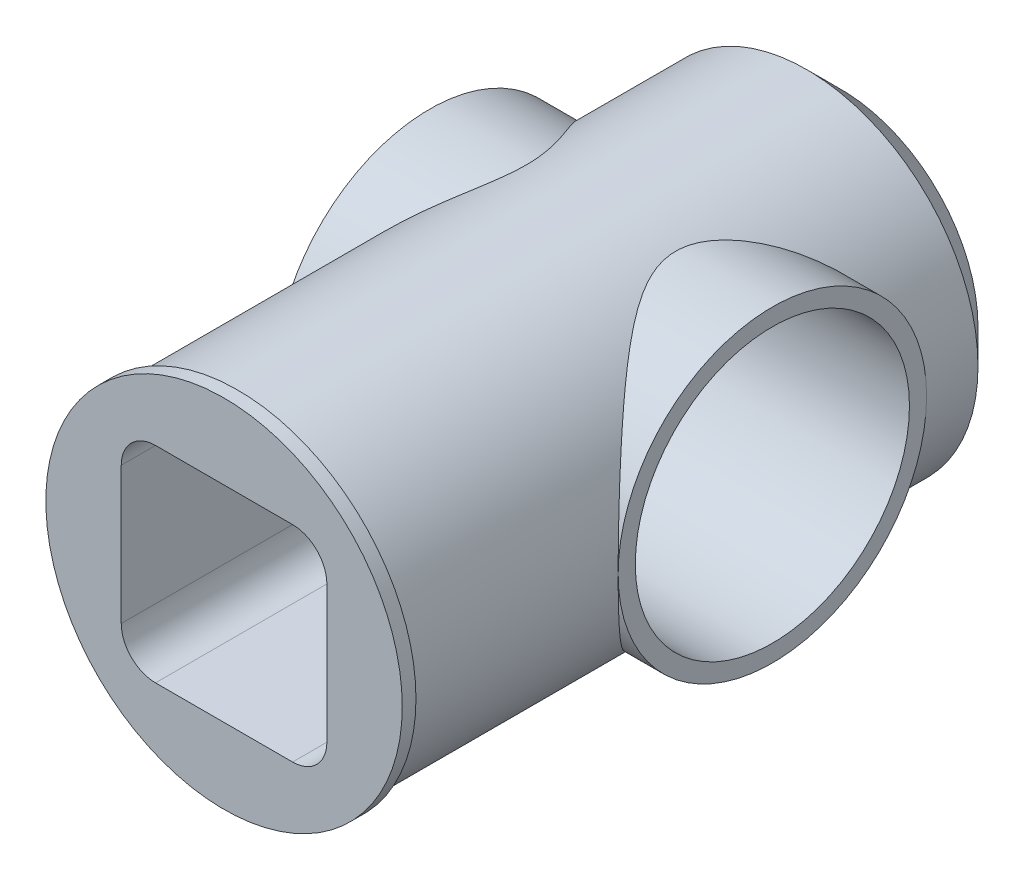
SolidWorks part; units mm, degrees
ref_plane "Front Plane" through (0, 0, 0) normal (0, 0, 1) x (1, 0, 0)
ref_plane "Top Plane" through (0, 0, 0) normal (0, 1, 0) x (1, 0, 0)
ref_plane "Right Plane" through (0, 0, 0) normal (1, 0, 0) x (0, 0, -1)
sketch "Sketch1" plane through (0, 0, 0) normal (0, 0, 1) x (1, 0, 0)
  circle A0 centre (0, 0) radius 25
  dimension "D1" = 50
extrude "Boss-Extrude3" add sketch "Sketch1" along normal blind 100
sketch "Sketch4" plane through (0, 0, 0) normal (1, 0, 0) x (0, 0, -1)
  circle A0 centre (-35, 0) radius 22.5
  dimension "D1" = 45
  dimension "D2" = 35
extrude "Boss-Extrude4" add sketch "Sketch4" along normal mid plane 50
sketch "Sketch5" plane through (25, 0, 0) normal (1, 0, 0) x (0, 0, -1)
  circle A0 centre (-35, 0) radius 20
  dimension "D1" = 40
extrude "Cut-Extrude2" cut sketch "Sketch5" against normal blind 50
chamfer "Chamfer1" distance 5 angle 45 1 edges at (25, 0, 0)
sketch "Sketch9" plane through (0, 0, 0) normal (1, 0, 0) x (0, 0, -1)
  line L1 (-100, 25) -> (-90, 25)
  line L2 (-100, 25) -> (-100, -35.1129)
  line L3 (-100, -35.1129) -> (-90, -35.1129)
  line L4 (-90, 25) -> (-90, -35.1129)
  dimension "D1" = 10
extrude "Cut-Extrude3" cut sketch "Sketch9" against normal through all both and the other way through all
sketch "Sketch11" plane through (0, 0, 90) normal (0, 0, 1) x (1, 0, 0)
  line L0 (-10, 15) -> (10, 15)
  line L1 (-15, 10) -> (-15, -10)
  line L2 (-10, -15) -> (10, -15)
  line L3 (15, 10) -> (15, -10)
  line L4 (-15, 15) -> (15, -15) construction
  line L5 (-15, -15) -> (15, 15) construction
  arc A0 (10, -15) -> (15, -10) centre (10, -10) ccw
  arc A1 (-15, -10) -> (-10, -15) centre (-10, -10) ccw
  arc A2 (10, 15) -> (15, 10) centre (10, 10) cw
  arc A3 (-10, 15) -> (-15, 10) centre (-10, 10) ccw
  point P0 (0, 0)
  dimension "D2" = 5
  dimension "D1" = 30
extrude "Cut-Extrude4" cut sketch "Sketch11" against normal blind 30
sketch "Sketch12" plane through (0, 0, 90) normal (0, 0, 1) x (1, 0, 0)
  circle A0 centre (0, 0) radius 26
  circle M9 centre (0, 0) radius 25
  dimension "D1" = 52
extrude "Boss-Extrude6" add sketch "Sketch12" against normal blind 2 contours A0 M9
